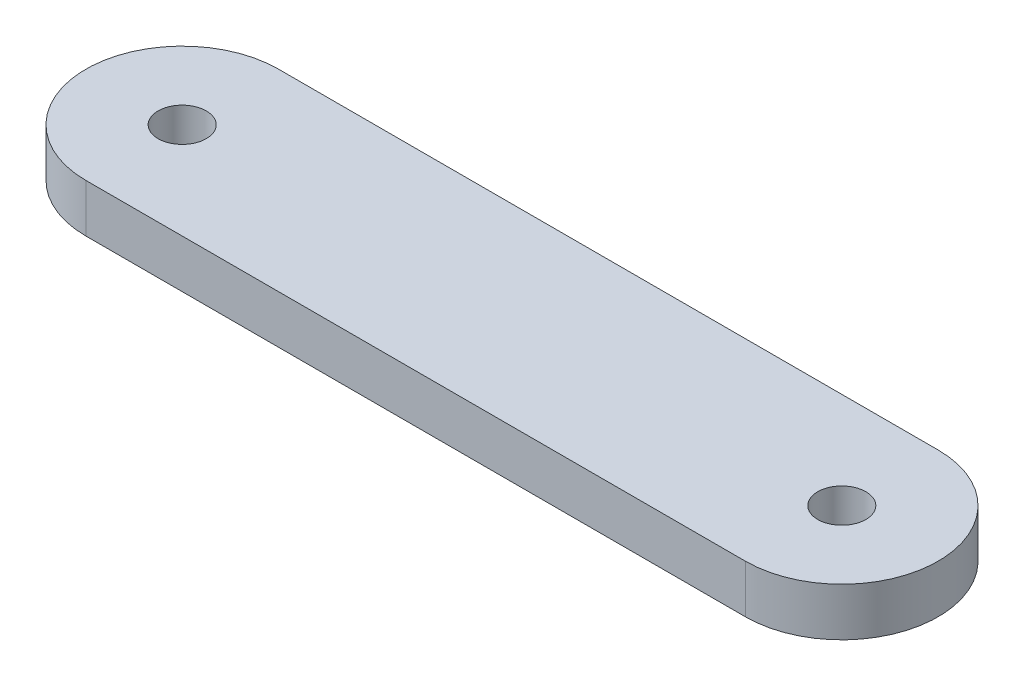
SolidWorks part; units mm, degrees
ref_plane "Front Plane" through (0, 0, 0) normal (0, 0, 1) x (1, 0, 0)
ref_plane "Top Plane" through (0, 0, 0) normal (0, 1, 0) x (1, 0, 0)
ref_plane "Right Plane" through (0, 0, 0) normal (1, 0, 0) x (0, 0, -1)
sketch "Sketch1" plane through (0, 0, 0) normal (0, 1, 0) x (1, 0, 0)
  line L0 (0, 0) -> (43.4726, 0) construction
  line L1 (0, 6.35) -> (43.4726, 6.35)
  line L2 (0, -6.35) -> (43.4726, -6.35)
  arc A1 (0, 6.35) -> (0, -6.35) centre (0, 0) ccw
  arc A2 (43.4726, -6.35) -> (43.4726, 6.35) centre (43.4726, 0) ccw
  circle A3 centre (0, 0) radius 1.5875
  circle A4 centre (43.4726, 0) radius 1.5875
  point P3 (21.7363, 0)
  dimension "D1" = 43.4726
  dimension "D3" = 3.175
  dimension "D4" = 3.175
  dimension "D2" = 12.7
extrude "Boss-Extrude1" add sketch "Sketch1" along normal blind 3.175
